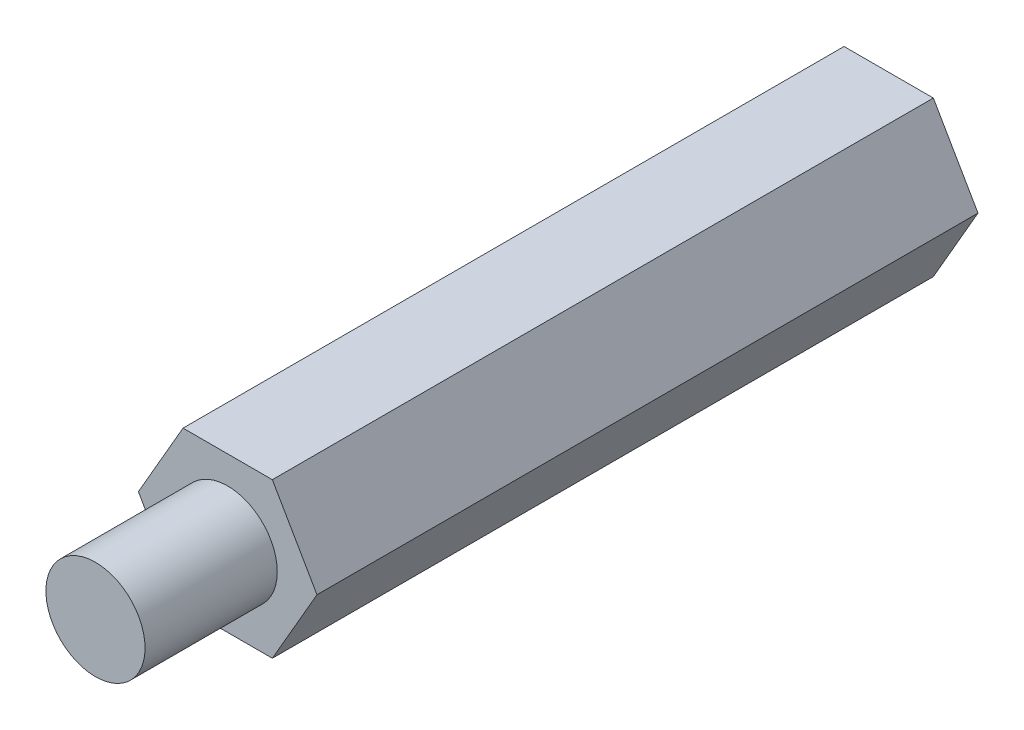
SolidWorks part; units mm, degrees
material "黃銅"
ref_plane "前基準面" through (0, 0, 0) normal (0, 0, 1) x (1, 0, 0)
ref_plane "上基準面" through (0, 0, 0) normal (0, 1, 0) x (1, 0, 0)
ref_plane "右基準面" through (0, 0, 0) normal (1, 0, 0) x (0, 0, -1)
sketch "草圖1" plane through (0, 0, 0) normal (0, 0, 1) x (1, 0, 0)
  line L1 (2.702, 0) -> (1.351, 2.34)
  line L2 (1.351, 2.34) -> (-1.351, 2.34)
  line L3 (-1.351, 2.34) -> (-2.702, 0)
  line L4 (-2.702, 0) -> (-1.351, -2.34)
  line L5 (-1.351, -2.34) -> (1.351, -2.34)
  line L6 (1.351, -2.34) -> (2.702, 0)
  circle A0 centre (0, 0) radius 2.34 construction
  point P1 (0, 0)
  dimension "D1" = 4.68
extrude "填料-伸長1" add sketch "草圖1" along normal blind 20
sketch "草圖2" plane through (0, 0, 20) normal (0, 0, 1) x (1, 0, 0)
  circle A0 centre (0, 0) radius 1.5
  dimension "D1" = 3
extrude "填料-伸長2" add sketch "草圖2" along normal blind 4
hole_wizard "M3x0.5 螺紋孔1" positions "草圖4" profile "草圖5" tap size "M3x0.5" standard "Ansi Metric"
sketch "草圖4" plane through (0, 0, 0) normal (0, 0, -1) x (-1, 0, 0)
  point P0 (0, 0)
sketch "草圖5" plane through (0, 0, 0) normal (1, 0, 0) x (0, 1, 0)
  line L0 (0, 0) -> (0, 5.7511)
  line L1 (0, 5.7511) -> (1.25, 5)
  line L2 (1.25, 5) -> (1.25, 0)
  line L5 (1.25, 0) -> (0, 0)
  line L10 (0, 5.7511) -> (-1.25, 5) construction
  line L11 (0, -6.35) -> (0, 107.95) construction
  dimension "螺孔鑽直徑" = 2.5
  dimension "螺孔鑽深度" = 5
  dimension "導頭角度" = 118
cosmetic thread "鑽孔螺紋1" parameters "D1"=6, "D2"=3
